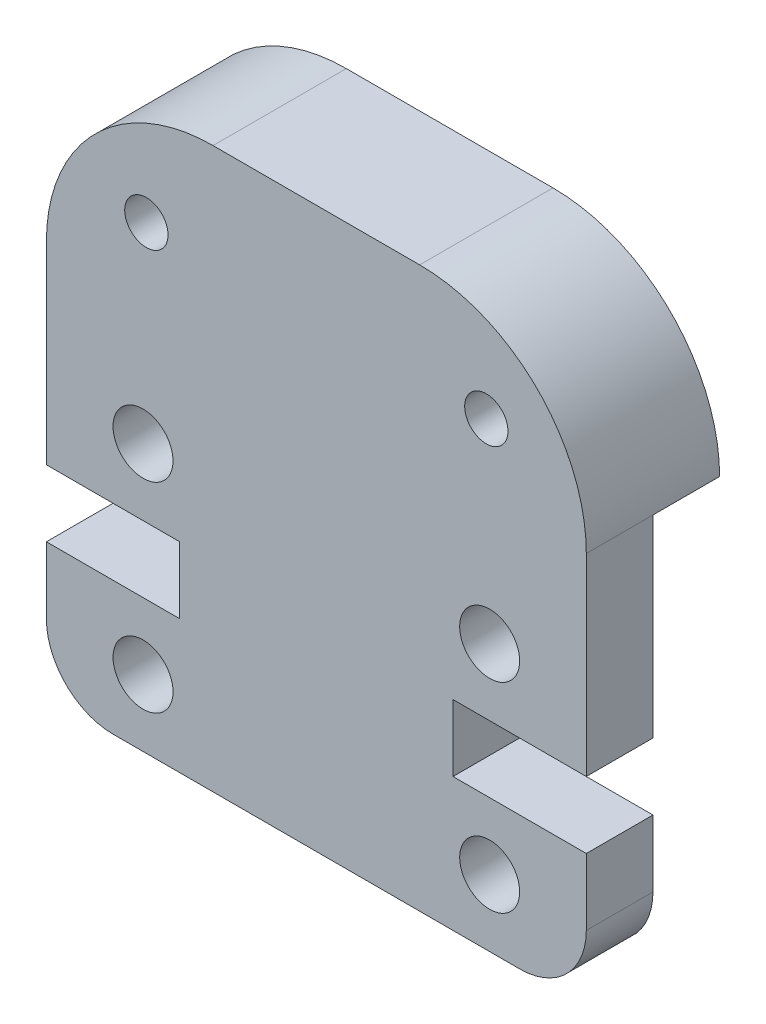
SolidWorks part; units mm, degrees
ref_plane "Front Plane" through (0, 0, 0) normal (0, 0, 1) x (1, 0, 0)
ref_plane "Top Plane" through (0, 0, 0) normal (0, 1, 0) x (1, 0, 0)
ref_plane "Right Plane" through (0, 0, 0) normal (1, 0, 0) x (0, 0, -1)
sketch "Sketch1" plane through (0, 0, 0) normal (0, 0, 1) x (1, 0, 0)
  line L0 (0, 6) -> (0, 11.795)
  line L1 (12.2, 4) -> (16.2, 4)
  line L2 (5, 16.795) -> (11.2, 16.795)
  line L3 (2, 0) -> (14.2, 0)
  line L4 (12.2, 6) -> (12.2, 4)
  line L5 (0, 2) -> (0, 4)
  line L6 (0, 6) -> (4, 6)
  line L7 (16.2, 6) -> (12.2, 6)
  line L8 (4, 6) -> (4, 4)
  line L9 (4, 4) -> (0, 4)
  line L10 (16.2, 2) -> (16.2, 4)
  line L11 (16.2, 6) -> (16.2, 11.795)
  line L12 (8.1, 16.795) -> (8.1, 0) construction
  circle A0 centre (13.3, 2) radius 0.9
  arc A1 (5, 16.795) -> (0, 11.795) centre (5, 11.795) ccw
  circle A2 centre (13.3, 8) radius 0.9
  circle A3 centre (3, 13.795) radius 0.65
  arc A4 (16.2, 2) -> (14.2, 0) centre (14.2, 2) cw
  arc A5 (0, 2) -> (2, 0) centre (2, 2) ccw
  circle A6 centre (13.2, 13.795) radius 0.65
  circle A7 centre (2.9, 8) radius 0.9
  arc A8 (11.2, 16.795) -> (16.2, 11.795) centre (11.2, 11.795) cw
  circle A9 centre (2.9, 2) radius 0.9
  dimension "D1" = 1.8
  dimension "D2" = 1.3
  dimension "D3" = 5
  dimension "D4" = 2
  dimension "D5" = 3
  dimension "D6" = 8.1
  dimension "D7" = 8
  dimension "D8" = 3
  dimension "D9" = 16.795
extrude "Boss-Extrude1" add sketch "Sketch1" along normal blind 4
sketch "Sketch2" plane through (0, 0, 0) normal (0, 0, 1) x (1, 0, 0)
  line L0 (0, 0) -> (0, 11.795)
  line L1 (0, 11.795) -> (16.2, 11.795)
  line L2 (16.2, 11.795) -> (16.2, 0)
  line L3 (16.2, 0) -> (0, 0)
extrude "Cut-Extrude1" cut sketch "Sketch2" along normal blind 2
equation "\"D6@Sketch1\"= \"fingerWidth@parametersSketch@prostheticParameters.SLDPRT\" / 2 'DIP width"
equation "\"D9@Sketch1\"= \"HL@parametersSketch@prostheticParameters.SLDPRT\" * 0.107 - 3 'DIP length - Sil. Sht DIP"
equation "\"D1@Sketch1\"= 1.5 + \"tol1@parametersSketch@prostheticParameters.SLDPRT\""
equation "\"D2@Sketch1\"= 1 + \"tol1@parametersSketch@prostheticParameters.SLDPRT\""
